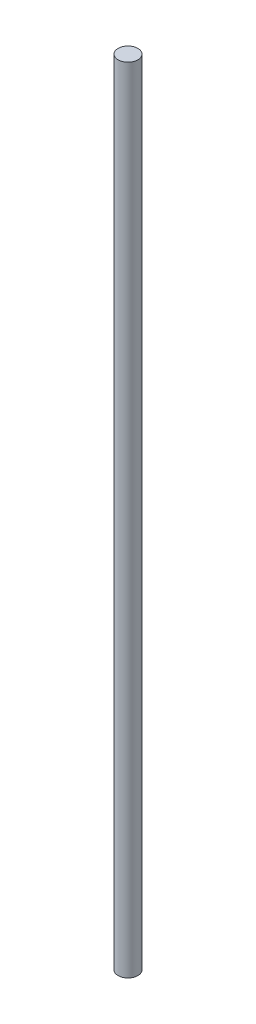
SolidWorks part; units mm, degrees
material "1060 Alloy"
ref_plane "Front Plane" through (0, 0, 0) normal (0, 0, 1) x (1, 0, 0)
ref_plane "Top Plane" through (0, 0, 0) normal (0, 1, 0) x (1, 0, 0)
ref_plane "Right Plane" through (0, 0, 0) normal (1, 0, 0) x (0, 0, -1)
sketch "Sketch1" plane through (0, 0, 0) normal (0, 1, 0) x (1, 0, 0)
  circle A1 centre (0, 0) radius 5
  dimension "D1" = 10
extrude "Boss-Extrude1" add sketch "Sketch1" along normal mid plane 400
